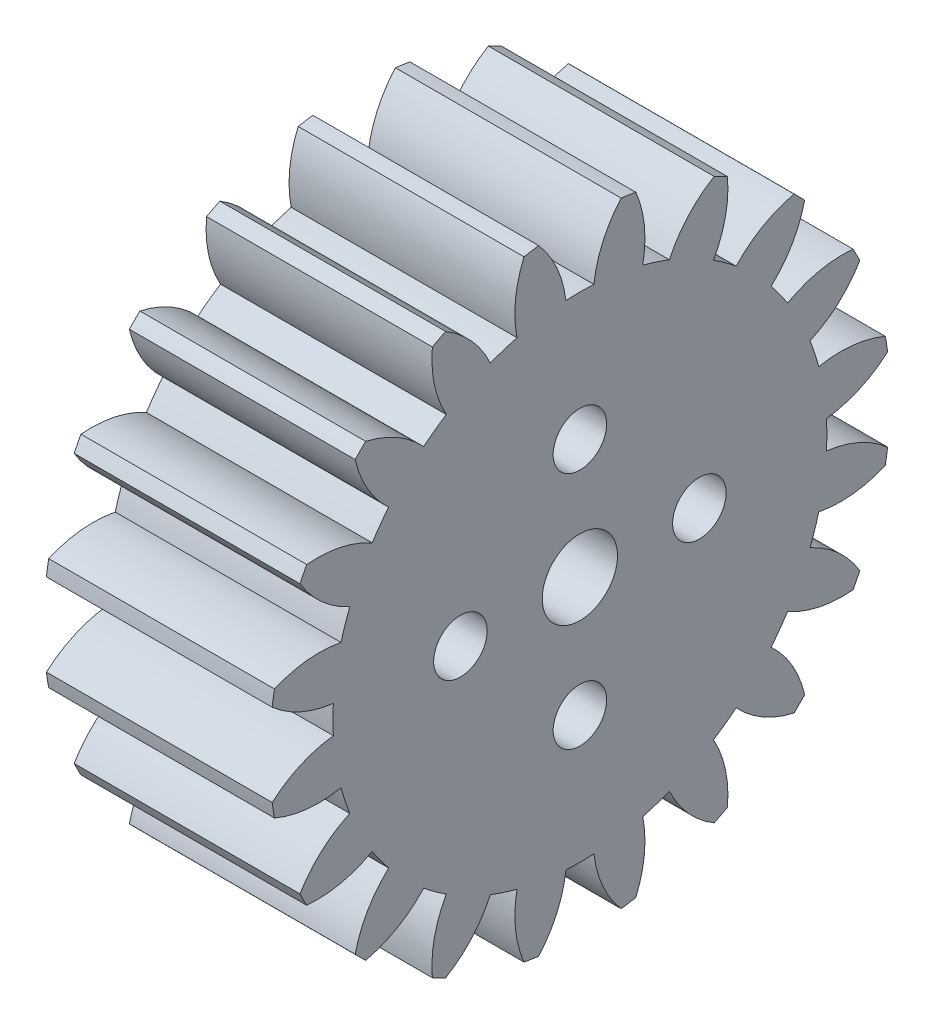
SolidWorks part; units mm, degrees
ref_plane "Plane1" through (0, 0, 0) normal (0, 0, 1) x (1, 0, 0)
ref_plane "Plane2" through (0, 0, 0) normal (0, 1, 0) x (1, 0, 0)
ref_plane "Plane3" through (0, 0, 0) normal (1, 0, 0) x (0, 0, -1)
sketch "HoldingSke" plane through (0, 0, 0) normal (0, 1, 0) x (1, 0, 0)
  line L0 (0, 0) -> (0.6265, -0.228)
  line L1 (-15, 0) -> (100, 0) construction
  line L2 (0, 0) -> (-2.1039, 2.3779)
  line L3 (0, 0) -> (-11.863, 4.5341)
  line L4 (0, 0) -> (8.1152, 2.9537)
  line L5 (0, 0) -> (-46.8476, -17.4728)
  line L6 (0, 0) -> (-9.9476, -6.7116)
  line L7 (-2.1039, 2.3779) -> (8.6586, 51.2059)
  line L8 (-76.2, 54.61) -> (-75.5, 54.61)
  line L9 (-71.009, 38.7566) -> (-53.1078, 45.2721)
  line L10 (-76.2, 71.12) -> (104.1128, 71.12)
  line L11 (0, 0) -> (-12, 0)
  line L12 (-76.2, 101.6) -> (-76.147, 101.6)
  line L13 (24.9733, 27.94) -> (52.9518, 28.4284)
  line L14 (24.9733, 27.94) -> (24.9743, 27.94)
  line L15 (24.9733, 27.94) -> (100.4006, 29.5858)
  line L16 (-63.627, -1.5) -> (-12.827, -1.5)
  circle A0 centre (0, 0) radius 2
  circle A1 centre (0, 0) radius 13.124
  circle A2 centre (0, 0) radius 37.5
  circle A3 centre (0, 0) radius 2
  dimension "MHD" = 26.248
  dimension "Hub_dia" = 75
  dimension "Bore" = 4
  dimension "MBD" = 4
  dimension "Num_teeth" = 20
  dimension "Pitch_radius" = 180.3128
  dimension "Pitch" = 0.6667
  dimension "Width" = 12
  dimension "Overall_len" = 50
  dimension "Show_teeth" = 20
  dimension "Thickness" = 12
  dimension "OAL" = 50.0001
  dimension "T_dim" = 0.7
  dimension "Ap" = 20
  dimension "H" = 19.05
  dimension "Backlash" = 0.053
  dimension "Addendum_fac" = 1
  dimension "Dedendum_fac" = 1.25
  dimension "Clearance_fac" = 0.25
  dimension "Dedendum_add" = 0.001
  dimension "Module" = 1.5
sketch "BasProSke" plane through (0, 0, 0) normal (0, 1, 0) x (1, 0, 0)
  line L0 (-10, 0) -> (60, 0) construction
  line L1 (0, 0) -> (0, 16.5)
  line L2 (0, 0) -> (12, 0)
  line L3 (12, 0) -> (12, 16.5)
  line L4 (12, 16.5) -> (0, 16.5)
  dimension "Diameter" = 33
  dimension "Thickness" = 12
revolve "Base-Revolve" add sketch "BasProSke" angle 360 about L0
sketch "TooCutSke" plane through (0, 0, 0) normal (1, 0, 0) x (0, 0, -1)
  line L1 (0, 0) -> (0, 107) construction
  line L2 (0, 0) -> (-1.2696, 14.9462) construction
  line L3 (0, 0) -> (-4.6808, 29.5532) construction
  line L4 (-1.2696, 14.9462) -> (-2.3404, 14.7766) construction
  arc A0 (0.7438, 13.1029) -> (-0.7438, 13.1029) centre (0, 0) ccw
  arc A1 (2.21, 16.377) -> (-2.21, 16.377) centre (0, 0) ccw
  circle A2 centre (0, 0) radius 15 construction
  circle A3 centre (0, 0) radius 14.0954 construction
  arc A4 (-0.7438, 13.1029) -> (-2.21, 16.377) centre (-6.7025, 12.3999) ccw
  arc A5 (2.21, 16.377) -> (0.7438, 13.1029) centre (6.7025, 12.3999) ccw
  dimension "Root_dia" = 26.248
  dimension "Overcut_dia" = 33.0508
  dimension "Pitch_dia" = 30
  dimension "Base_dia" = 28.1908
  dimension "Flank_rad" = 6
  dimension "Half_ang" = 9
  dimension "Half_CT" = 1.0841
extrude "ToothCut" cut sketch "TooCutSke" along normal through all
fillet "Breaks" [suppressed] radius 0.03
fillet "RootFillets" [suppressed] radius 0.376
pattern_circular "TeethCuts" count 20 every 18 about axis through (-10, 0, 0) along (1, 0, 0) of "ToothCut", "RootFillets", "Breaks"
sketch "HubNeaOneSke" plane through (0, 0, 0) normal (-1, 0, 0) x (0, 0, 1)
  circle A0 centre (0, 0) radius 13.124
  dimension "Diameter" = 26.248
extrude "HubNearOne" [suppressed] add sketch "HubNeaOneSke" along normal blind 38.0001
sketch "HubNeaBotSke" plane through (0, 0, 0) normal (-1, 0, 0) x (0, 0, 1)
  circle A0 centre (0, 0) radius 13.124
  dimension "Diameter" = 26.248
extrude "HubNearBoth" [suppressed] add sketch "HubNeaBotSke" along normal blind 19
ref_plane "FarPln" through (12, 0, 0) normal (1, 0, 0) x (0, 0, -1)
sketch "HubFarSke" plane through (12, 0, 0) normal (1, 0, 0) x (0, 0, -1)
  circle A0 centre (0, 0) radius 13.124
  dimension "Diameter" = 26.248
extrude "HubFar" [suppressed] add sketch "HubFarSke" along normal blind 19
sketch "BorSke" plane through (0, 0, 0) normal (1, 0, 0) x (0, 0, -1)
  circle A0 centre (0, 0) radius 2
  dimension "Diameter" = 4
extrude "Bore" cut sketch "BorSke" along normal mid plane 100.0001
sketch "KeySke" plane through (0, 0, 0) normal (1, 0, 0) x (0, 0, -1)
  line L0 (-0.8, 0) -> (-0.8, 2.7)
  line L1 (-0.8, 2.7) -> (0.8, 2.7)
  line L2 (0.8, 2.7) -> (0.8, 0)
  line L3 (0, 0) -> (0, 34) construction
  line L4 (-0.8, 0) -> (0.8, 0)
  dimension "Offset" = 2.7
  dimension "Width" = 1.6
extrude "Keyway" [suppressed] cut sketch "KeySke" along normal mid plane 100.0001
pattern_circular "Keyway2" [suppressed] count 2 every 90 about axis through (-10, 0, 0) along (1, 0, 0)
sketch "Sketch1" plane through (0, 0, 0) normal (1, 0, 0) x (0, 0, -1)
  circle A0 centre (0, 6.35) radius 1.4224
  circle A1 centre (0, 0) radius 2 construction
  circle A2 centre (6.35, 0) radius 1.4224
  circle A3 centre (0, -6.35) radius 1.4224
  circle A4 centre (-6.35, 0) radius 1.4224
  point P13 (0, 0)
  dimension "D1" = 6.35
extrude "Cut-Extrude1" cut sketch "Sketch1" along normal through all
equation "' \"Module@HoldingSke\" = 6.35"
equation "' \"Num_teeth@HoldingSke\" = 12"
equation "' \"Ap@HoldingSke\" =  20"
equation "' \"Width@HoldingSke\" = 0.5 * 25.4"
equation "' \"Hub_dia@HoldingSke\"= 1 * 25.4"
equation "' \"Overall_len@HoldingSke\" = 1.0 * 25.4"
equation "' \"Bore@HoldingSke\" = 0.75 * 25.4"
equation "' \"T_dim@HoldingSke\" = 0.1 * 25.4"
equation "' \"Width@KeySke\" = 0.25 * 25.4"
equation "' \"Show_teeth@HoldingSke\" = 13"
equation "' \"Backlash@HoldingSke\" = 0.009 * 25.4"
equation "' \"Addendum_fac@HoldingSke\" = 1.0"
equation "' \"Dedendum_fac@HoldingSke\" = 1.25"
equation "' \"Dedendum_add@HoldingSke\" = 0.00005 * 25.4"
equation "' \"Clearance_fac@HoldingSke\" = 0.25"
equation "\"Pitch@HoldingSke\" = 1 / \"Module@HoldingSke\""
equation "\"Overcut_dia@TooCutSke\" = (\"Num_teeth@HoldingSke\" + 2 * \"Addendum_fac@HoldingSke\") / \"Pitch@HoldingSke\" + 0.002 * 25.4"
equation "\"Pitch_dia@TooCutSke\" = \"Num_teeth@HoldingSke\" / \"Pitch@HoldingSke\""
equation "\"Base_dia@TooCutSke\" = \"Num_teeth@HoldingSke\" / \"Pitch@HoldingSke\" * cos((\"Ap@HoldingSke\"  * 3.14159265 / 180))"
equation "\"Root_dia@TooCutSke\" = (\"Num_teeth@HoldingSke\" + 2) / \"Pitch@HoldingSke\" - 2 * (\"Addendum_fac@HoldingSke\" + \"Dedendum_fac@HoldingSke\") / \"Pitch@HoldingSke\" - \"Dedendum_add@HoldingSke\" * 2"
equation "\"Half_ang@TooCutSke\" = 180 / \"Num_teeth@HoldingSke\""
equation "\"Half_CT@TooCutSke\" = \"Num_teeth@HoldingSke\" / \"Pitch@HoldingSke\" * sin((3.14159265 / 2 / \"Num_teeth@HoldingSke\")) / 2 - 7 * \"Backlash@HoldingSke\" / 4"
equation "\"Flank_rad@TooCutSke\" = \"Num_teeth@HoldingSke\" / \"Pitch@HoldingSke\" / 5"
equation "\"Radius@RootFillets\" = \"Clearance_fac@HoldingSke\" / \"Pitch@HoldingSke\" + \"Dedendum_add@HoldingSke\""
equation "\"Break_rad@Breaks\" = 0.02 / \"Pitch@HoldingSke\""
equation "\"Thickness@HoldingSke\" = \"Width@HoldingSke\""
equation "\"OAL@HoldingSke\" = \"Thickness@HoldingSke\""
equation "\"MHD@HoldingSke\" = (\"Num_teeth@HoldingSke\" + 2) / \"Pitch@HoldingSke\" - 2 * (\"Addendum_fac@HoldingSke\" + \"Dedendum_fac@HoldingSke\")  / \"Pitch@HoldingSke\" - \"Dedendum_add@HoldingSke\" * 2"
equation "\"MBD@HoldingSke\" = (\"Num_teeth@HoldingSke\" + 2) / \"Pitch@HoldingSke\" - 2 * (\"Addendum_fac@HoldingSke\" + \"Dedendum_fac@HoldingSke\")  / \"Pitch@HoldingSke\" - \"Dedendum_add@HoldingSke\" * 2 - 0.002 * 25.4"
equation "\"MHD@HoldingSke\" = ((sgn( \"MHD@HoldingSke\" - \"Hub_dia@HoldingSke\" )-1)*( \"MHD@HoldingSke\" - \"Hub_dia@HoldingSke\" ))/-2+ \"Hub_dia@HoldingSke\""
equation "\"MBD@HoldingSke\" = ((sgn( \"MBD@HoldingSke\" - \"Bore@HoldingSke\" )-1)*( \"MBD@HoldingSke\" - \"Bore@HoldingSke\" ))/-2+ \"Bore@HoldingSke\""
equation "\"OAL@HoldingSke\" = ((sgn( \"OAL@HoldingSke\" - \"Overall_len@HoldingSke\" )+1)*( \"OAL@HoldingSke\" - \"Overall_len@HoldingSke\" ))/2 + \"Overall_len@HoldingSke\" + 0.000002 * 25.4"
equation "\"Num_teeth@TeethCuts\" = int( \"Show_teeth@HoldingSke\" ) + 1"
equation "\"Num_teeth@TeethCuts\" = ((sgn( \"Num_teeth@TeethCuts\" - \"Num_teeth@HoldingSke\" )-1)*( \"Num_teeth@TeethCuts\" - \"Num_teeth@HoldingSke\" ))/-2+ \"Num_teeth@HoldingSke\""
equation "\"Num_teeth@TeethCuts\" = ((sgn( \"Num_teeth@TeethCuts\" - 2.0)+1)*( \"Num_teeth@TeethCuts\" - 2.0))/2 +2.0"
equation "\"Angle@TeethCuts\" = 360.0 / \"Num_teeth@HoldingSke\""
equation "\"Diameter@BasProSke\" = (\"Num_teeth@HoldingSke\" + 2 * \"Addendum_fac@HoldingSke\") / \"Pitch@HoldingSke\""
equation "\"Thickness@BasProSke\"  = \"Thickness@HoldingSke\""
equation "' \"Fillet_rad@BasProSke\" =  \"Thickness@HoldingSke\" * 0.05"
equation "\"MHD@HoldingSke\" = ((sgn( \"MHD@HoldingSke\" - \"Root_dia@TooCutSke\" )-1)*( \"MHD@HoldingSke\" - \"Root_dia@TooCutSke\" ))/-2+ \"Root_dia@TooCutSke\""
equation "\"Diameter@HubNeaOneSke\" = \"MHD@HoldingSke\""
equation "\"Length@HubNearOne\" = \"OAL@HoldingSke\" - \"Thickness@BasProSke\""
equation "\"Diameter@HubNeaBotSke\" = \"MHD@HoldingSke\""
equation "\"Length@HubNearBoth\" = ( \"OAL@HoldingSke\" - \"Thickness@BasProSke\" ) / 2.0"
equation "\"Thickness@FarPln\" = \"Thickness@BasProSke\""
equation "\"Diameter@HubFarSke\" = \"MHD@HoldingSke\""
equation "\"Length@HubFar\" = ( \"OAL@HoldingSke\" - \"Thickness@BasProSke\" ) / 2.0"
equation "\"Diameter@BorSke\" = \"MBD@HoldingSke\""
equation "\"D1@Bore\" = \"OAL@HoldingSke\" * 2.0"
equation "\"D1@Keyway\" = \"OAL@HoldingSke\" * 2.0"
equation "\"Offset@KeySke\" = \"T_dim@HoldingSke\" + \"MBD@HoldingSke\" / 2.0"
